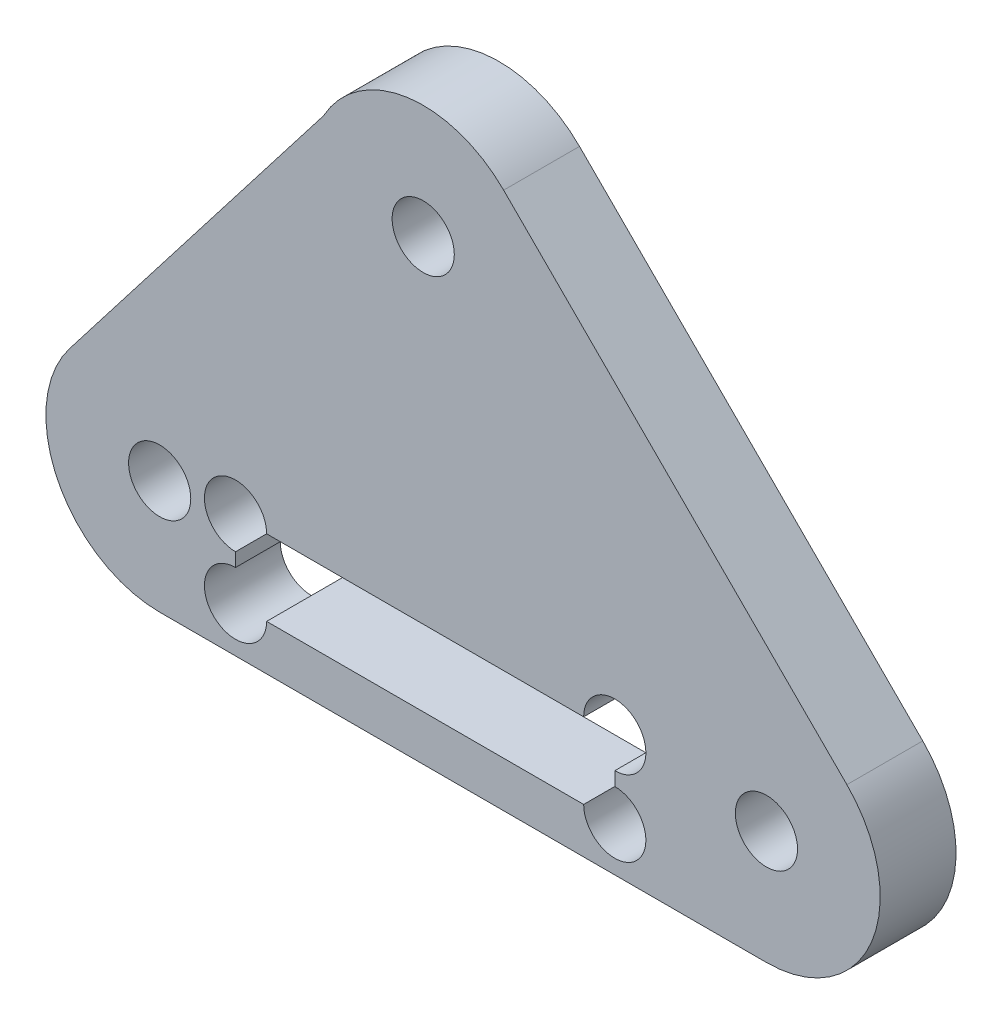
SolidWorks part; units mm, degrees
material "Acrílico (Impacto medio-alto)"
ref_plane "Piano frontale" through (0, 0, 0) normal (0, 0, 1) x (1, 0, 0)
ref_plane "Piano superiore" through (0, 0, 0) normal (0, 1, 0) x (1, 0, 0)
ref_plane "Piano destro" through (0, 0, 0) normal (1, 0, 0) x (0, 0, -1)
sketch "Schizzo1" plane through (0, 0, 0) normal (0, 0, 1) x (1, 0, 0)
  line L0 (-22.6274, -7.5) -> (0, -7.5)
  line L1 (-22.6274, 22.6274) -> (0, 0) construction
  line L2 (0, 0) -> (-22.6274, 0) construction
  line L3 (-29.2018, 26.2367) -> (-30.1227, 0.2658) construction
  line L4 (-17.3241, 27.9307) -> (5.3033, 5.3033)
  line L5 (-22.6274, 22.6274) -> (-22.6274, 0) construction
  line L6 (-45.9343, 4.5863) -> (-29.2018, 26.2367)
  line L7 (-10, -4.5) -> (-35, -4.5)
  line L8 (-10, -4.5) -> (-10, 0.5)
  line L9 (-10, 0.5) -> (-35, 0.5)
  line L10 (-35, -4.5) -> (-35, 0.5)
  line L11 (-10, -4.5) -> (-35, 0.5) construction
  line L12 (-10, 0.5) -> (-35, -4.5) construction
  line L13 (-40, -7.5) -> (-22.6274, -7.5)
  line L14 (-22.6274, 0) -> (-40, 0) construction
  line L15 (-40, 0) -> (-22.6274, 22.6274) construction
  circle A0 centre (0, 0) radius 2.05
  arc A1 (0, -7.5) -> (5.3033, 5.3033) centre (0, 0) ccw
  arc A2 (-29.2018, 26.2367) -> (-17.3241, 27.9307) centre (-22.6274, 22.6274) cw
  arc A3 (-30.1227, 0.2658) -> (-22.6274, -7.5) centre (-22.6274, 0) ccw construction
  circle A4 centre (-22.6274, 22.6274) radius 2.05
  circle A5 centre (-40, 0) radius 2.05
  arc A6 (-40, -7.5) -> (-45.9343, 4.5863) centre (-40, 0) cw
  point P5 (-22.5, -2)
  dimension "D1" = 4.1
  dimension "D2" = 90
  dimension "D3" = 5
  dimension "D4" = 3
  dimension "D7" = 7.5
  dimension "D8" = 10
  dimension "D9" = 40
  dimension "D10" = 32
  dimension "D12" = 7.5
  dimension "D13" = 7.5
  dimension "D5" = 25
  dimension "D11" = 45
extrude "Estrusione-Estrusione2" add sketch "Schizzo1" along normal blind 5
sketch "Sketch1" plane through (0, 0, 5) normal (0, 0, 1) x (1, 0, 0)
  circle A0 centre (-35, 0.5) radius 2.05
  circle A1 centre (-35, -4.5) radius 2.05
  circle A2 centre (-10, -4.5) radius 2.05
  circle A3 centre (-10, 0.5) radius 2.05
  dimension "D1" = 4.1
extrude "Cut-Extrude1" cut sketch "Sketch1" against normal up to next
